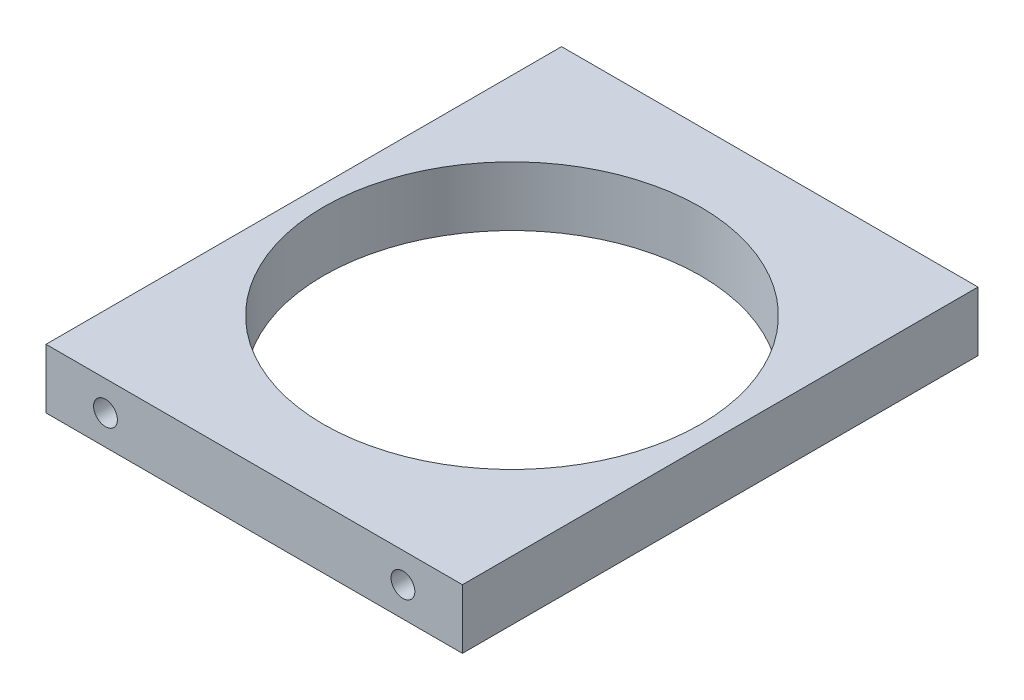
SolidWorks part; units mm, degrees
ref_plane "Front Plane" through (0, 0, 0) normal (0, 0, 1) x (1, 0, 0)
ref_plane "Top Plane" through (0, 0, 0) normal (0, 1, 0) x (1, 0, 0)
ref_plane "Right Plane" through (0, 0, 0) normal (1, 0, 0) x (0, 0, -1)
sketch "Sketch1" plane through (0, 0, 0) normal (0, 1, 0) x (1, 0, 0)
  line L1 (21, -26) -> (-21, -26)
  line L2 (21, -26) -> (21, 26)
  line L3 (21, 26) -> (-21, 26)
  line L4 (-21, -26) -> (-21, 26)
  line L5 (21, -26) -> (-21, 26) construction
  line L6 (21, 26) -> (-21, -26) construction
  point P0 (0, 0)
  dimension "D1" = 42
  dimension "D2" = 52
extrude "Boss-Extrude1" add sketch "Sketch1" along normal mid plane 6
sketch "Sketch2" plane through (0, 3, 0) normal (0, 1, 0) x (1, 0, 0)
  circle A0 centre (0, 0) radius 19
  dimension "D1" = 38
extrude "Cut-Extrude1" cut sketch "Sketch2" against normal through all
sketch "Sketch3" plane through (0, 0, -26) normal (0, 0, -1) x (-1, 0, 0)
  line L0 (-21, 3) -> (-21, -3) construction
  circle A0 centre (-15, 0) radius 1.2
  circle A1 centre (15, 0) radius 1.2
  dimension "D1" = 2.4
  dimension "D2" = 6
  dimension "D3" = 30
extrude "Cut-Extrude2" cut sketch "Sketch3" against normal blind 8
sketch "Sketch4" plane through (0, 0, 26) normal (0, 0, 1) x (1, 0, 0)
  circle A0 centre (15, 0) radius 1.2
  circle A1 centre (-15, 0) radius 1.2
extrude "Cut-Extrude3" cut sketch "Sketch4" against normal blind 8
